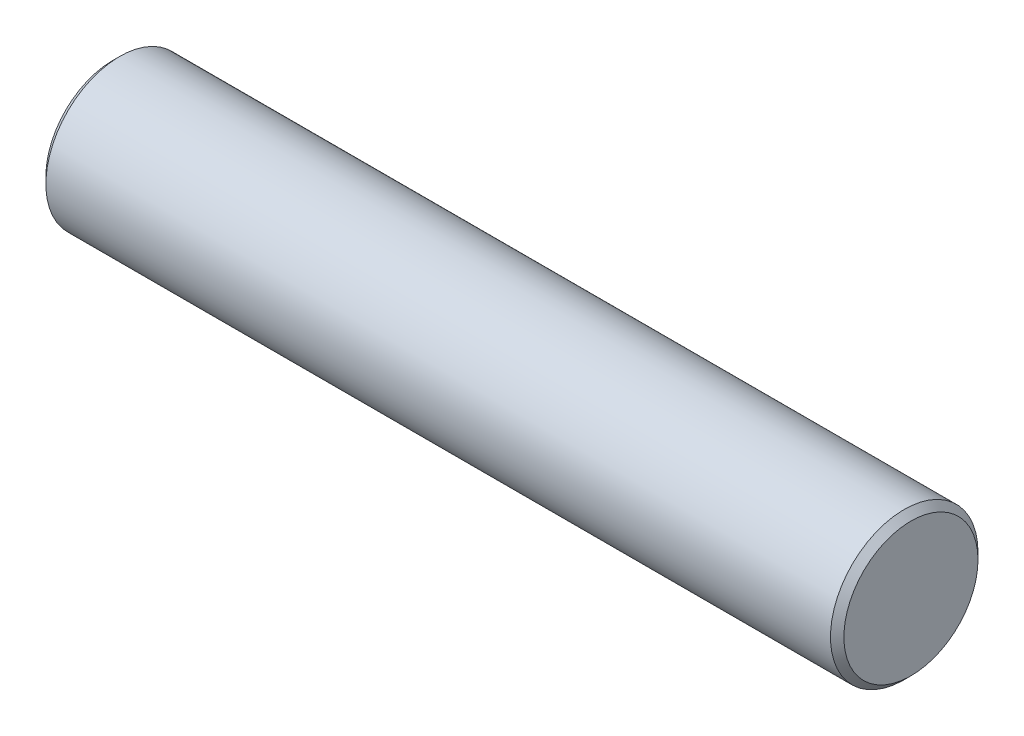
SolidWorks part; units mm, degrees
ref_plane "Front Plane" through (0, 0, 0) normal (0, 0, 1) x (1, 0, 0)
ref_plane "Top Plane" through (0, 0, 0) normal (0, 1, 0) x (1, 0, 0)
ref_plane "Right Plane" through (0, 0, 0) normal (1, 0, 0) x (0, 0, -1)
sketch "Sketch1" plane through (0, 0, 0) normal (1, 0, 0) x (0, 0, -1)
  circle A0 centre (0, 0) radius 11
  dimension "D1" = 22
extrude "Boss-Extrude1" add sketch "Sketch1" along normal mid plane 119
chamfer "Chamfer1" distance 1 angle 45 2 edges at (-59.5, 0, -11) (59.5, 0, -11)
